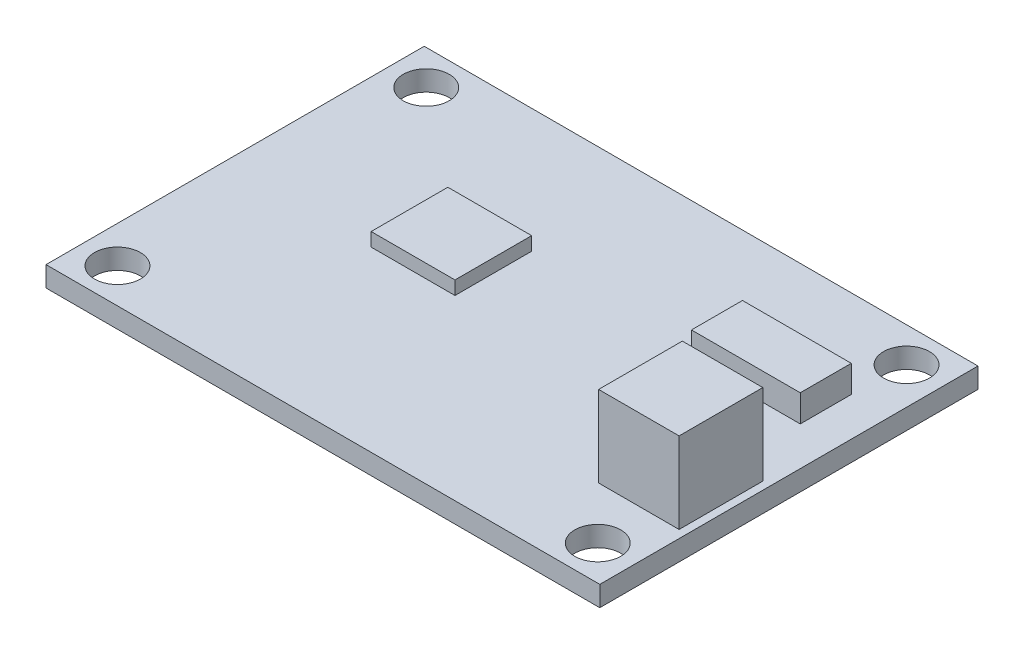
SolidWorks part; units mm, degrees
material "Elaborazione scheda, Semplice"
ref_plane "Piano frontale" through (0, 0, 0) normal (0, 0, 1) x (1, 0, 0)
ref_plane "Piano superiore" through (0, 0, 0) normal (0, 1, 0) x (1, 0, 0)
ref_plane "Piano destro" through (0, 0, 0) normal (1, 0, 0) x (0, 0, -1)
sketch "Schizzo1" plane through (0, 0, 0) normal (0, 1, 0) x (1, 0, 0)
  line L1 (20.5, -14) -> (-20.5, -14)
  line L2 (20.5, -14) -> (20.5, 14)
  line L3 (20.5, 14) -> (-20.5, 14)
  line L4 (-20.5, -14) -> (-20.5, 14)
  line L5 (20.5, -14) -> (-20.5, 14) construction
  line L6 (20.5, 14) -> (-20.5, -14) construction
  point P0 (0, 0)
  dimension "D1" = 41
  dimension "D2" = 28
extrude "Estrusione-Estrusione1" add sketch "Schizzo1" along normal blind 1.5
hole_wizard "Foro per Vite M3-1" positions "Schizzo3" profile "Schizzo2" hole size "M3" standard "Ansi Metric" end condition through all
sketch "Schizzo3" plane through (0, 1.5, 0) normal (0, 1, 0) x (1, 0, 0)
  line L0 (-17.78, 11.43) -> (17.78, 11.43) construction
  line L1 (17.78, 11.43) -> (17.78, -11.43) construction
  line L2 (17.78, -11.43) -> (-17.78, -11.43) construction
  line L3 (-17.78, -11.43) -> (-17.78, 11.43) construction
  line L4 (-17.78, 11.43) -> (17.78, -11.43) construction
  point P0 (17.78, -11.43)
  point P2 (17.78, 11.43)
  point P4 (-17.78, 11.43)
  point P6 (-17.78, -11.43)
  dimension "D1" = 22.86
  dimension "D2" = 35.56
sketch "Schizzo2" plane through (17.78, 1.5, 11.43) normal (1, 0, 0) x (0, 0, 1)
  line L0 (0, 0) -> (0, 1.5)
  line L1 (0, 1.5) -> (1.7, 1.5)
  line L2 (1.7, 1.5) -> (1.7, 0)
  line L5 (1.7, 0) -> (0, 0)
  line L11 (0, -6.35) -> (0, 107.95) construction
  dimension "Thru Hole Dia." = 3.4
  dimension "Thru Hole Depth" = 1.5
sketch "Schizzo5" plane through (0, 1.5, 0) normal (0, 1, 0) x (1, 0, 0)
  line L1 (-3.3798, -0.8423) -> (-9.5861, -0.8423)
  line L2 (-3.3798, -0.8423) -> (-3.3798, 4.8362)
  line L3 (-3.3798, 4.8362) -> (-9.5861, 4.8362)
  line L4 (-9.5861, -0.8423) -> (-9.5861, 4.8362)
  line L5 (-3.3798, -0.8423) -> (-9.5861, 4.8362) construction
  line L6 (-3.3798, 4.8362) -> (-9.5861, -0.8423) construction
  point P0 (-6.4829, 1.997)
extrude "Estrusione-Estrusione2" add sketch "Schizzo5" along normal blind 1
sketch "Schizzo6" plane through (0, 1.5, 0) normal (0, 1, 0) x (1, 0, 0)
  line L1 (13.9582, -7.5461) -> (19.9165, -7.5461)
  line L2 (13.9582, -7.5461) -> (13.9582, -1.3478)
  line L3 (13.9582, -1.3478) -> (19.9165, -1.3478)
  line L4 (19.9165, -7.5461) -> (19.9165, -1.3478)
  line L5 (13.9582, -7.5461) -> (19.9165, -1.3478) construction
  line L6 (13.9582, -1.3478) -> (19.9165, -7.5461) construction
  point P0 (16.9374, -4.447)
extrude "Estrusione-Estrusione3" add sketch "Schizzo6" along normal blind 6
sketch "Schizzo7" plane through (0, 1.5, 0) normal (0, 1, 0) x (1, 0, 0)
  line L1 (9.581, 7.4819) -> (17.6361, 7.4819)
  line L2 (9.581, 7.4819) -> (9.581, 3.7048)
  line L3 (9.581, 3.7048) -> (17.6361, 3.7048)
  line L4 (17.6361, 7.4819) -> (17.6361, 3.7048)
  line L5 (9.581, 7.4819) -> (17.6361, 3.7048) construction
  line L6 (9.581, 3.7048) -> (17.6361, 7.4819) construction
  point P0 (13.6085, 5.5934)
extrude "Estrusione-Estrusione4" add sketch "Schizzo7" along normal blind 2
